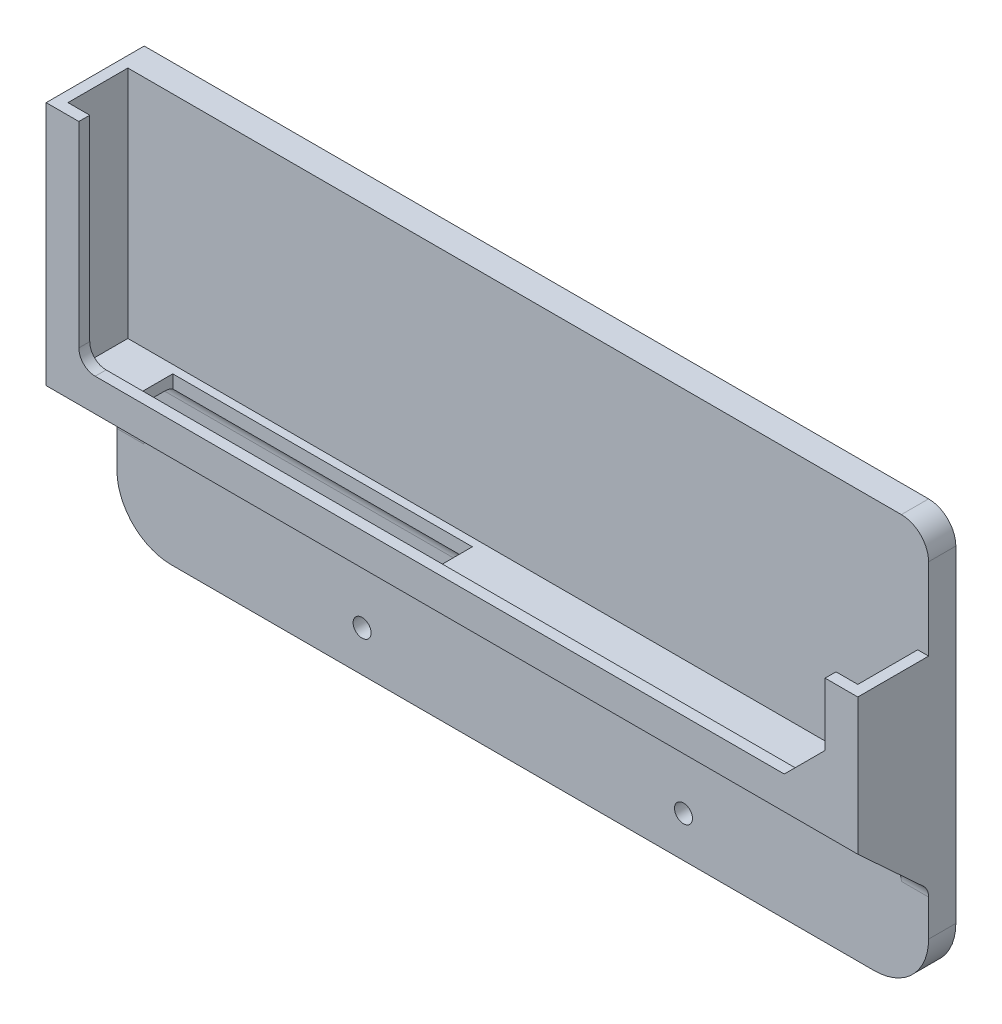
SolidWorks part; units mm, degrees
ref_plane "Front Plane" through (0, 0, 0) normal (0, 0, 1) x (1, 0, 0)
ref_plane "Top Plane" through (0, 0, 0) normal (0, 1, 0) x (1, 0, 0)
ref_plane "Right Plane" through (0, 0, 0) normal (1, 0, 0) x (0, 0, -1)
sketch "Sketch1" plane through (0, 0, 0) normal (0, 0, 1) x (1, 0, 0)
  line L1 (0, 0) -> (149, 0)
  line L2 (0, 0) -> (0, 15)
  line L3 (0, 15) -> (149, 15)
  line L4 (149, 0) -> (149, 15)
  line L5 (0, 15) -> (149, 15)
  line L6 (0, 15) -> (0, 75)
  line L7 (0, 75) -> (149, 75)
  line L8 (149, 15) -> (149, 75)
  circle A0 centre (45, 7.5) radius 1.65
  circle A1 centre (104, 7.5) radius 1.65
  dimension "D4" = 3.3
  dimension "D5" = 3.3
  dimension "D1" = 15
  dimension "D2" = 149
  dimension "D3" = 60
  dimension "D6" = 45
  dimension "D7" = 45
  dimension "D8" = 149
extrude "Boss-Extrude1" add sketch "Sketch1" along normal blind 5 contours L3 L8 L7 L6 | L1 L4 L3 L2
fillet "Fillet1" radius 10 2 edges at (149, 0, 2.5) (0, 0, 2.5)
sketch "Sketch2" plane through (0, 0, 5) normal (0, 0, 1) x (1, 0, 0)
  line L0 (149, 10) -> (149, 75) construction
  line L1 (0, 75) -> (2, 75)
  line L2 (0, 75) -> (0, 30)
  line L3 (0, 30) -> (149, 30)
  line L4 (149, 55) -> (149, 30)
  line L5 (2, 73) -> (2, 32)
  line L6 (2, 32) -> (147, 32)
  line L7 (147, 55) -> (147, 32)
  line L9 (2, 73) -> (2, 75)
  line L12 (0, 75) -> (149, 75) construction
  line L13 (2, 73) -> (147, 73) construction
  line L14 (147, 73) -> (147, 32) construction
  line L19 (149, 75) -> (149, 30) construction
  line L20 (0, 75) -> (149, 75) construction
  line L23 (149, 55) -> (147, 55)
  dimension "D1" = 45
  dimension "D2" = 2
  dimension "D3" = 20
extrude "Boss-Extrude2" add sketch "Sketch2" along normal blind 11
sketch "Sketch3" plane through (0, 0, 16) normal (0, 0, 1) x (1, 0, 0)
  line L0 (149, 30) -> (149, 55) construction
  line L1 (0, 75) -> (0, 30) construction
  line L2 (0, 30) -> (149, 30) construction
  line L3 (149, 30) -> (149, 55)
  line L4 (0, 75) -> (0, 30)
  line L5 (0, 30) -> (149, 30)
  line L6 (6, 75) -> (6, 36)
  line L7 (6, 36) -> (143, 36)
  line L8 (143, 36) -> (143, 55)
  line L9 (6, 75) -> (0, 75)
  line L10 (143, 55) -> (149, 55)
  dimension "D1" = 6
extrude "Boss-Extrude3" add sketch "Sketch3" along normal blind 2 contours L6 L7 L8 L10 L3 L5 L4 L9
chamfer "Chamfer1" distance 7.5 angle 45 1 edges at (143, 36, 17)
sketch "Sketch4" plane through (0, 0, 0) normal (-1, 0, 0) x (0, 0, 1)
  line L0 (18, 30) -> (5, 18)
  line L1 (5, 10) -> (5, 30) construction
  line L2 (18, 30) -> (5, 30)
  line L3 (5, 30) -> (5, 18)
extrude "Boss-Extrude4" add sketch "Sketch4" against normal blind 5 contours L0 L3 L2
ref_plane "Plane1" through (74.5, 0, 0) normal (-1, 0, 0) x (0, 0, 1)
mirror "Mirror1" about plane through (74.5, 0, 0) normal (-1, 0, 0) of "Boss-Extrude4"
fillet "Fillet2" radius 3 3 edges at (146.5, 18, 5) (74.5, 30, 5) (2.5, 18, 5)
sketch "Sketch5" plane through (0, 32, 0) normal (0, 1, 0) x (1, 0, 0)
  line L0 (74.5, -5) -> (74.5, -16)
  line L1 (147, -5) -> (2, -5) construction
  line L2 (147, -16) -> (2, -16) construction
  line L4 (11.7411, -14.5) -> (66.7411, -14.5)
  line L5 (11.7411, -14.5) -> (11.7411, -6.5)
  line L6 (11.7411, -6.5) -> (66.7411, -6.5)
  line L7 (66.7411, -14.5) -> (66.7411, -6.5)
  line L8 (11.7411, -14.5) -> (66.7411, -6.5) construction
  line L9 (11.7411, -6.5) -> (66.7411, -14.5) construction
  point P6 (39.2411, -10.5)
  dimension "D1" = 8
  dimension "D2" = 55
extrude "Cut-Extrude1" cut sketch "Sketch5" against normal blind 10 contours L4 L7 L6 L5
fillet "Fillet3" radius 3 1 edges at (6, 36, 17)
fillet "Fillet4" radius 5 1 edges at (149, 75, 2.5)
